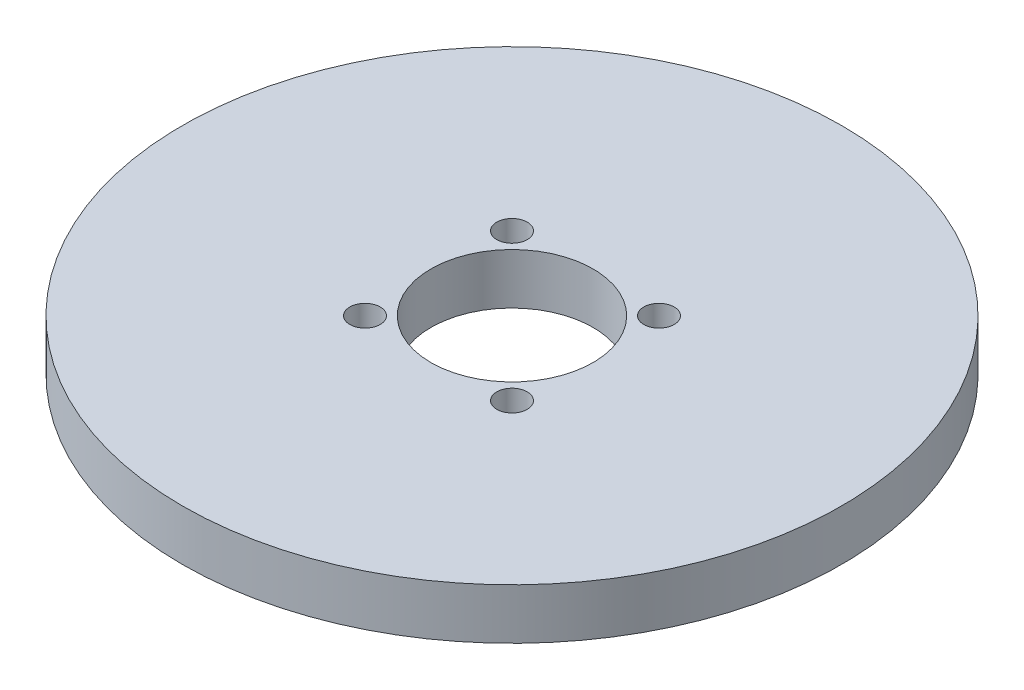
SolidWorks part; units mm, degrees
ref_plane "Front Plane" through (0, 0, 0) normal (0, 0, 1) x (1, 0, 0)
ref_plane "Top Plane" through (0, 0, 0) normal (0, 1, 0) x (1, 0, 0)
ref_plane "Right Plane" through (0, 0, 0) normal (1, 0, 0) x (0, 0, -1)
sketch "Sketch1" plane through (0, 0, 0) normal (0, 1, 0) x (1, 0, 0)
  line L0 (0, 0) -> (0, 12.5) construction
  line L1 (0, 0) -> (-8.8388, 8.8388) construction
  line L2 (0, 0) -> (-8.8388, -8.8388) construction
  circle A0 centre (0, 0) radius 32.5
  circle A1 centre (0, 0) radius 8
  circle A2 centre (0, 0) radius 12.5 construction
  circle A3 centre (0, 0) radius 10.25 construction
  circle A4 centre (-7.2478, 7.2478) radius 1.5
  circle A5 centre (7.2478, 7.2478) radius 1.5
  circle A6 centre (7.2478, -7.2478) radius 1.5
  circle A7 centre (-7.2478, -7.2478) radius 1.5
  point P11 (0, 0)
  point P20 (0, 0)
  dimension "D1" = 65
  dimension "D2" = 16
  dimension "D3" = 25
  dimension "D4" = 20.5
  dimension "D5" = 45
  dimension "D6" = 3
  dimension "D7" = 4
extrude "Boss-Extrude1" add sketch "Sketch1" along normal blind 5
